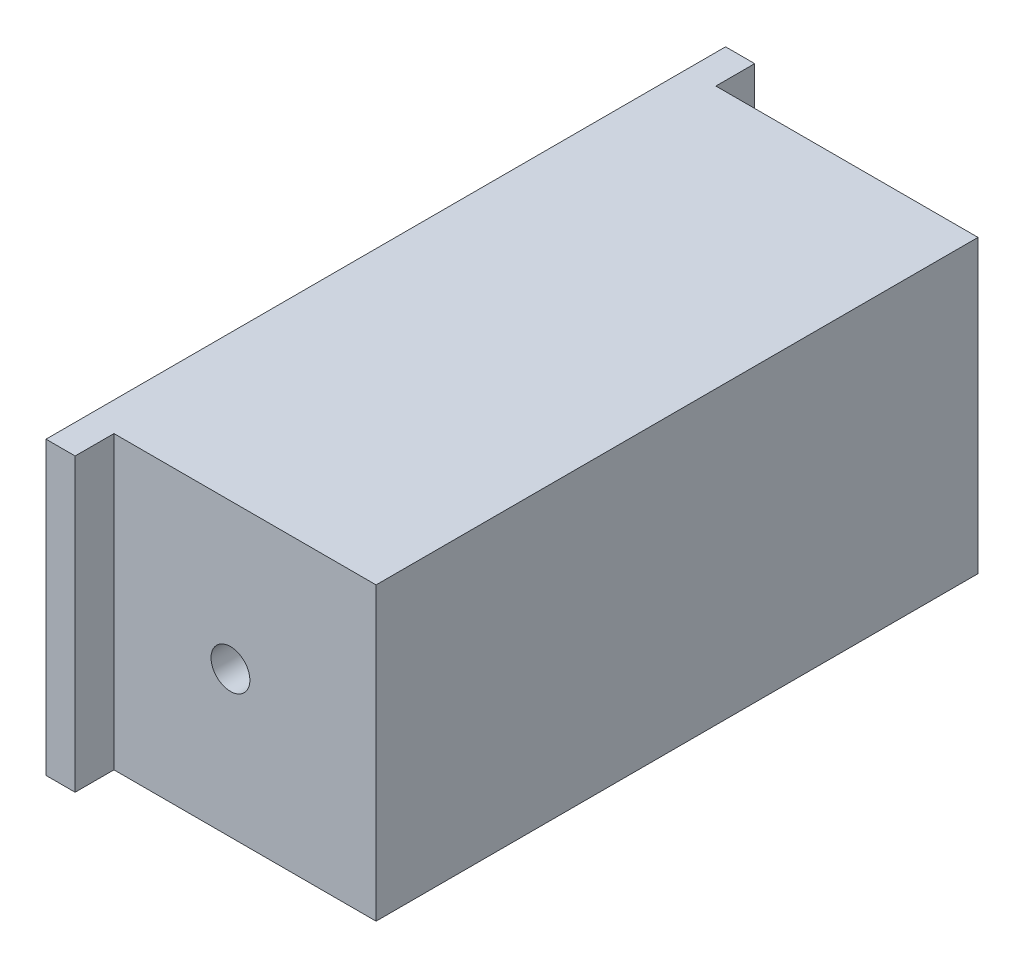
SolidWorks part; units mm, degrees
ref_plane "Front Plane" through (0, 0, 0) normal (0, 0, 1) x (1, 0, 0)
ref_plane "Top Plane" through (0, 0, 0) normal (0, 1, 0) x (1, 0, 0)
ref_plane "Right Plane" through (0, 0, 0) normal (1, 0, 0) x (0, 0, -1)
sketch "Sketch1" plane through (0, 0, 0) normal (1, 0, 0) x (0, 0, -1)
  line L1 (-155, 75) -> (155, 75)
  line L2 (-155, 75) -> (-155, -75)
  line L3 (-155, -75) -> (155, -75)
  line L4 (155, 75) -> (155, -75)
  line L5 (-155, 75) -> (155, -75) construction
  line L6 (-155, -75) -> (155, 75) construction
  point P0 (0, 0)
  dimension "D1" = 310
  dimension "D2" = 150
extrude "Boss-Extrude1" add sketch "Sketch1" along normal blind 150
sketch "Sketch2" plane through (0, 0, -155) normal (0, 0, -1) x (-1, 0, 0)
  circle A0 centre (-75, 0) radius 10
  dimension "D1" = 20
extrude "Cut-Extrude1" cut sketch "Sketch2" against normal blind 65
sketch "Sketch3" plane through (0, 0, -155) normal (0, 0, -1) x (-1, 0, 0)
  line L0 (-150, -75) -> (0, -75) construction
  line L1 (0, 75) -> (-15, 75)
  line L2 (0, 75) -> (0, -75)
  line L3 (0, -75) -> (-15, -75)
  line L4 (-15, 75) -> (-15, -75)
  dimension "D1" = 15
extrude "Boss-Extrude2" add sketch "Sketch3" along normal blind 20
mirror "Mirror1" about plane through (0, 0, 0) normal (0, 0, 1) of "Cut-Extrude1", "Boss-Extrude2"
sketch "Sketch4" plane through (0, 0, 0) normal (-1, 0, 0) x (0, 0, 1)
  text T0 "Crusher" font "Clarendon Blk BT" height in points 150
extrude "Cut-Extrude3" cut sketch "Sketch4" against normal blind 10
